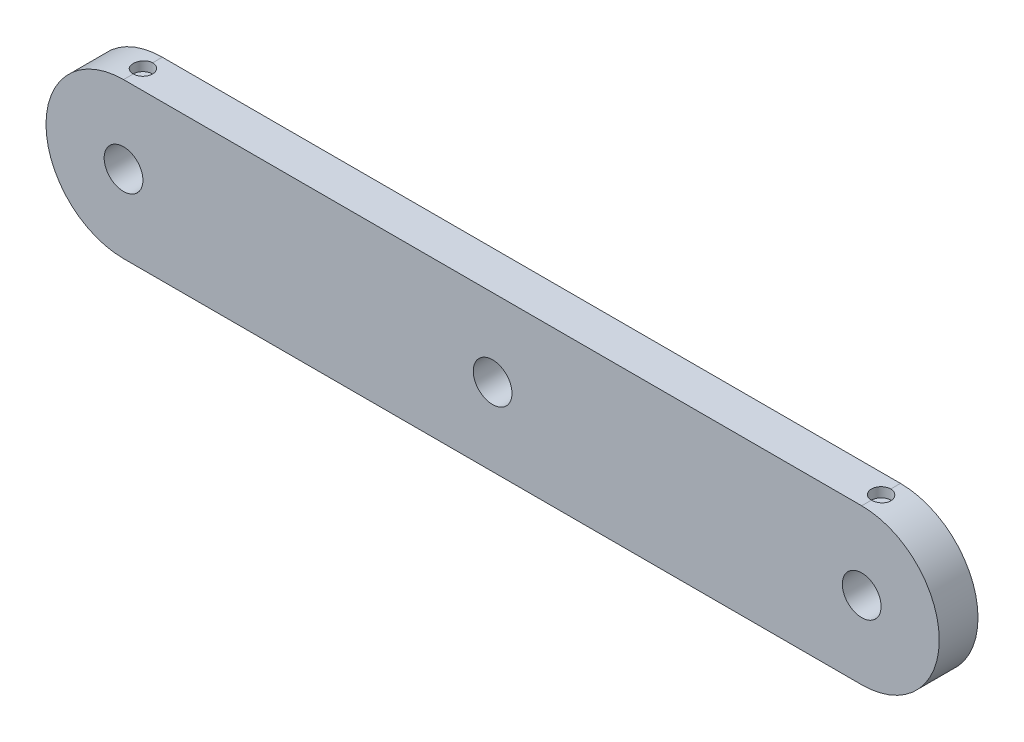
SolidWorks part; units mm, degrees
ref_plane "Front Plane" through (0, 0, 0) normal (0, 0, 1) x (1, 0, 0)
ref_plane "Top Plane" through (0, 0, 0) normal (0, 1, 0) x (1, 0, 0)
ref_plane "Right Plane" through (0, 0, 0) normal (1, 0, 0) x (0, 0, -1)
sketch "Sketch1" plane through (0, 0, 0) normal (0, 0, 1) x (1, 0, 0)
  line L2 (-19.042, 4) -> (19.042, 4)
  line L3 (-19.042, -4) -> (19.042, -4)
  circle A5 centre (0, 0) radius 1
  circle A6 centre (19.042, 0) radius 1
  circle A7 centre (-19.042, 0) radius 1
  arc A8 (19.042, -4) -> (19.042, 4) centre (19.042, 0) ccw
  arc A9 (-19.042, 4) -> (-19.042, -4) centre (-19.042, 0) ccw
  dimension "D1" = 2
  dimension "D2" = 4
  dimension "D3" = 19.042
  dimension "D4" = 19.042
extrude "Boss-Extrude1" add sketch "Sketch1" along normal blind 2
sketch "Sketch2" plane through (0, 4, 0) normal (0, 1, 0) x (1, 0, 0)
  line L0 (-19.042, -2) -> (-19.042, 0) construction
  circle A0 centre (-19.042, -1) radius 0.5
  circle A1 centre (19.042, -1) radius 0.5
extrude "Cut-Extrude1" cut sketch "Sketch2" against normal blind 0.5
sketch "Sketch3" plane through (0, -4, 0) normal (0, -1, 0) x (1, 0, 0)
  circle A0 centre (0, 1) radius 0.5
extrude "Cut-Extrude2" cut sketch "Sketch3" against normal blind 0.5
